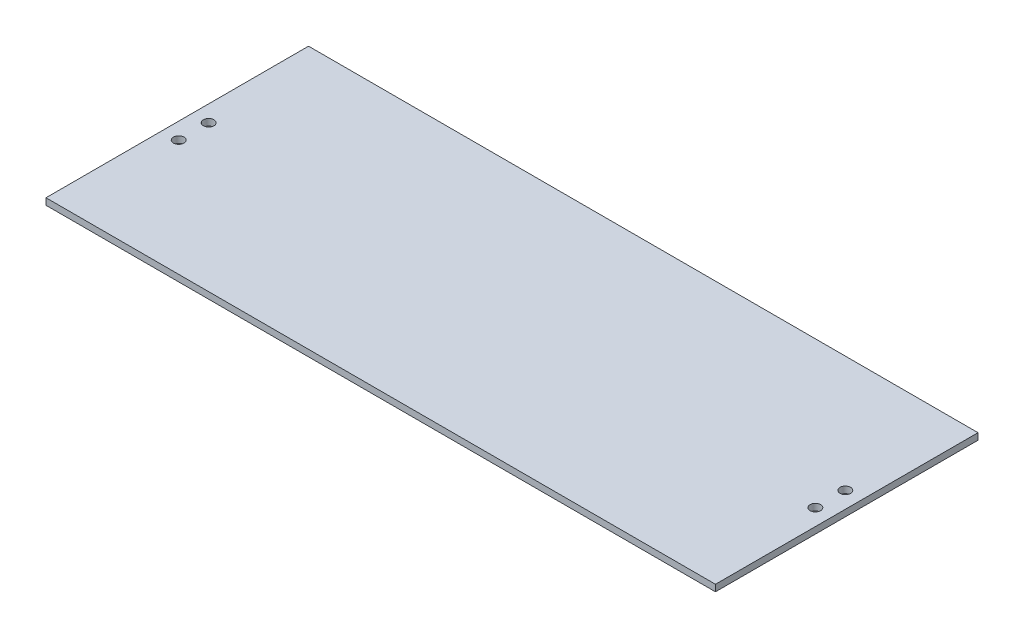
SolidWorks part; units mm, degrees
material "6061-T6 (SS)"
ref_plane "Front Plane" through (0, 0, 0) normal (0, 0, 1) x (1, 0, 0)
ref_plane "Top Plane" through (0, 0, 0) normal (0, 1, 0) x (1, 0, 0)
ref_plane "Right Plane" through (0, 0, 0) normal (1, 0, 0) x (0, 0, -1)
sketch "Sketch1" plane through (0, 0, 0) normal (0, 1, 0) x (1, 0, 0)
  line L1 (0, 0) -> (323.85, 0)
  line L2 (0, 0) -> (0, 127)
  line L3 (0, 127) -> (323.85, 127)
  line L4 (323.85, 0) -> (323.85, 127)
  dimension "D1" = 127
  dimension "D2" = 323.85
extrude "Boss-Extrude1" add sketch "Sketch1" along normal blind 3.175
hole_wizard "#10 Clearance Hole1" positions "Sketch3" profile "Sketch2" hole size "#10" standard "ANSI Inch" end condition through all
sketch "Sketch3" plane through (0, 0, 0) normal (0, -1, 0) x (-1, 0, 0)
  point P0 (-315.9125, 56.25)
  point P3 (-315.9125, 70.75)
  point P6 (-7.9375, 70.75)
  point P9 (-7.9375, 56.25)
sketch "Sketch2" plane through (315.9125, 0, -56.25) normal (1, 0, 0) x (0, 0, -1)
  line L0 (0, 0) -> (0, 3.175)
  line L1 (0, 3.175) -> (2.5527, 3.175)
  line L2 (2.5527, 3.175) -> (2.5527, 0)
  line L5 (2.5527, 0) -> (0, 0)
  line L11 (0, -6.35) -> (0, 107.95) construction
  dimension "Thru Hole Dia." = 5.1054
  dimension "Thru Hole Depth" = 3.175
